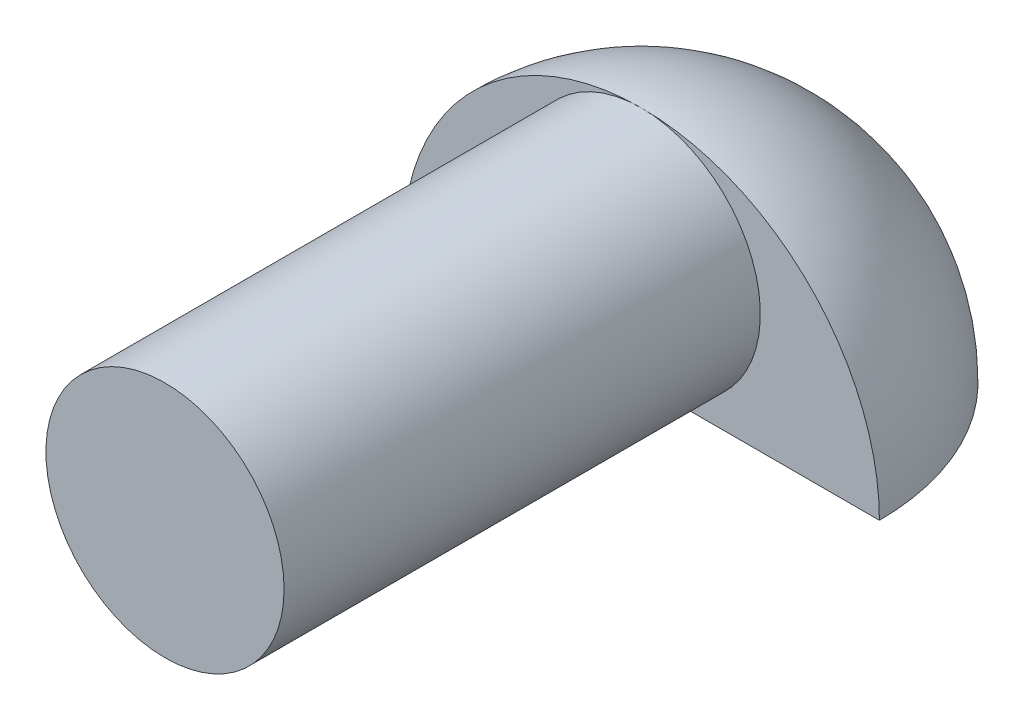
SolidWorks part; units mm, degrees
material "1060 Alloy"
ref_plane "Front Plane" through (0, 0, 0) normal (0, 0, 1) x (1, 0, 0)
ref_plane "Top Plane" through (0, 0, 0) normal (0, 1, 0) x (1, 0, 0)
ref_plane "Right Plane" through (0, 0, 0) normal (1, 0, 0) x (0, 0, -1)
sketch "Sketch7" plane through (0, 0, 0) normal (0, 0, 1) x (1, 0, 0)
  line L0 (-19.05, 0) -> (0, 0)
  line L1 (0, 19.05) -> (0, 0)
  arc A0 (0, 19.05) -> (-19.05, 0) centre (0, 0) ccw
  dimension "D1" = 19.05
revolve "Revolve2" add sketch "Sketch7" angle 180 about L1
sketch "Sketch8" plane through (0, 0, 0) normal (0, 0, 1) x (1, 0, 0)
  line L0 (19.05, 0) -> (-19.05, 0) construction
  circle A0 centre (0, 9.525) radius 9.525
  dimension "D1" = 19.05
extrude "Boss-Extrude4" add sketch "Sketch8" along normal blind 38.1 contours A0
